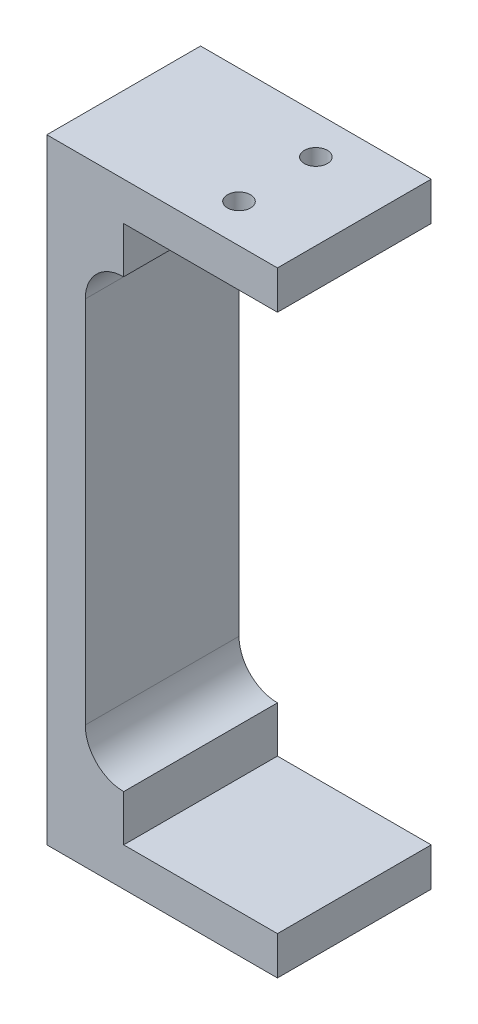
SolidWorks part; units mm, degrees
ref_plane "Front Plane" through (0, 0, 0) normal (0, 0, 1) x (1, 0, 0)
ref_plane "Top Plane" through (0, 0, 0) normal (0, 1, 0) x (1, 0, 0)
ref_plane "Right Plane" through (0, 0, 0) normal (1, 0, 0) x (0, 0, -1)
sketch "Sketch1" plane through (0, 0, 0) normal (0, 0, 1) x (1, 0, 0)
  line L0 (20, 0) -> (-10, 0)
  line L1 (-10, 0) -> (-10, -80)
  line L2 (-10, -80) -> (20, -80)
  line L3 (20, -80) -> (20, -75)
  line L4 (20, -75) -> (-5, -75)
  line L7 (20, -5) -> (20, 0)
  line L8 (-5, -75) -> (-5, -5)
  line L9 (-5, -5) -> (20, -5)
  dimension "D1" = 30
  dimension "D2" = 80
  dimension "D3" = 30
  dimension "D4" = 5
  dimension "D5" = 5
  dimension "D6" = 25
  dimension "D7" = 5
extrude "Boss-Extrude1" add sketch "Sketch1" along normal blind 20
sketch "Sketch3" plane through (0, 0, 0) normal (0, 0, 1) x (1, 0, 0)
  line L1 (-5, -75) -> (-5, -5) construction
  line L3 (-5, -5) -> (20, -5) construction
  line L4 (0, -5) -> (-5, -5)
  line L5 (0, -5) -> (0, -11)
  line L7 (-5, -75) -> (0, -75)
  line L8 (20, -75) -> (-5, -75) construction
  line L9 (0, -75) -> (0, -69)
  line L12 (0, -69) -> (0, -64) construction
  line L13 (-5, -64) -> (0, -64) construction
  line L14 (-5, -75) -> (-5, -64)
  line L15 (-19.7737, -40) -> (49.108, -40) construction
  line L16 (0, -16) -> (0, -11) construction
  line L17 (-5, -16) -> (0, -16) construction
  line L18 (-5, -5) -> (-5, -16)
  arc A0 (0, -69) -> (-5, -64) centre (0, -64) cw
  arc A1 (0, -11) -> (-5, -16) centre (0, -16) ccw
  dimension "D1" = 11
  dimension "D2" = 5
  dimension "D3" = 11
  dimension "D4" = 5
  dimension "D5" = 5
  dimension "D6" = 5
extrude "Boss-Extrude2" add sketch "Sketch3" along normal blind 20
sketch "Sketch4" plane through (0, 0, 0) normal (0, 1, 0) x (1, 0, 0)
  line L1 (20, -20) -> (20, 0) construction
  line L3 (-10, -10) -> (20, -10) construction
  line L4 (-10, -20) -> (-10, 0) construction
  circle A0 centre (10, -5) radius 1.5
  circle A1 centre (10, -15) radius 1.5
  dimension "D1" = 3
  dimension "D2" = 3
  dimension "D3" = 10
  dimension "D4" = 10
  dimension "D5" = 5
extrude "Cut-Extrude1" cut sketch "Sketch4" against normal up to surface (5 mm away) up to face at (10, -5, 10)
